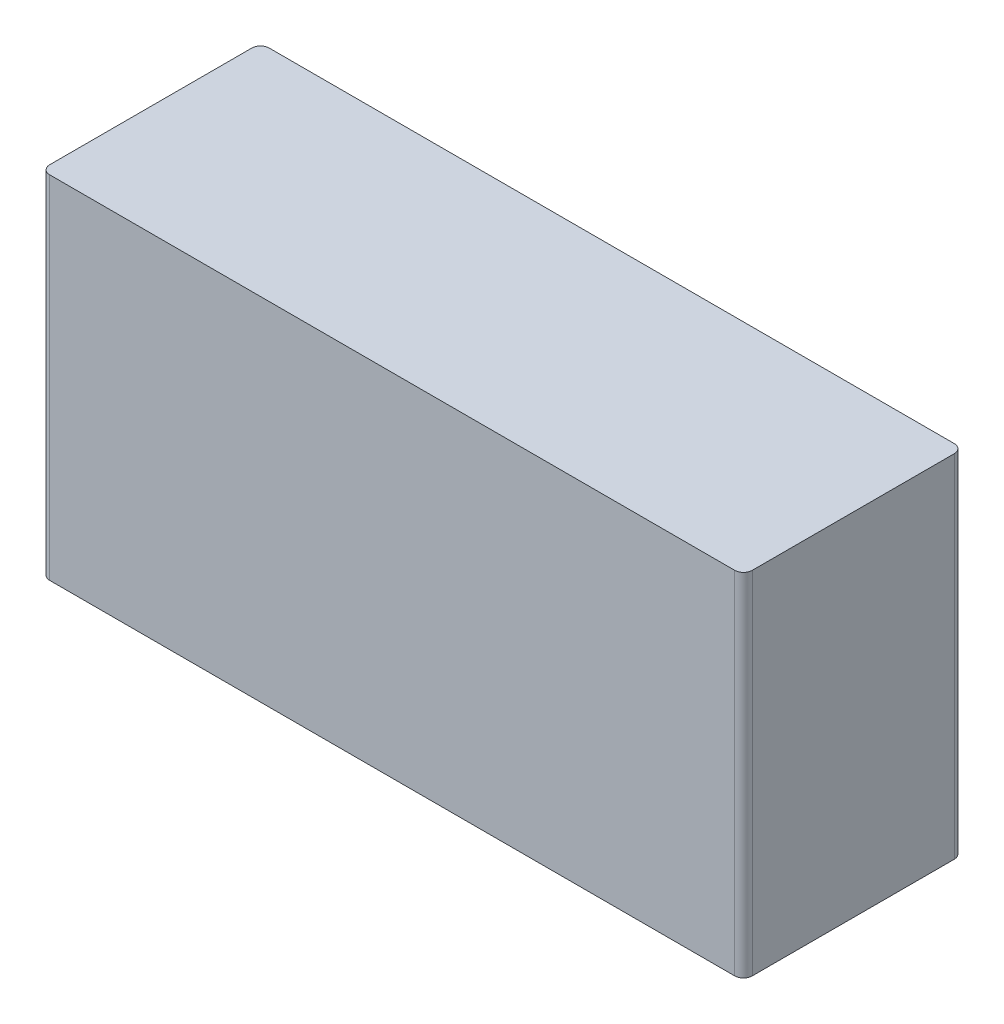
SolidWorks part; units mm, degrees
ref_plane "Alzado" through (0, 0, 0) normal (0, 0, 1) x (1, 0, 0)
ref_plane "Planta" through (0, 0, 0) normal (0, 1, 0) x (1, 0, 0)
ref_plane "Vista lateral" through (0, 0, 0) normal (1, 0, 0) x (0, 0, -1)
sketch "Sketch1" plane through (0, 0, 0) normal (0, 0, 1) x (1, 0, 0)
  line L1 (0, 0) -> (80, 0)
  line L2 (0, 0) -> (0, 40)
  line L3 (0, 40) -> (80, 40)
  line L4 (80, 0) -> (80, 40)
  dimension "D1" = 80
  dimension "D2" = 40
extrude "Boss-Extrude1" add sketch "Sketch1" along normal blind 25
fillet "Fillet3" radius 1 1 edges at (0, 20, 25)
fillet "Fillet4" radius 1 3 edges at (0, 20, 0) (80, 20, 0) (80, 20, 25)
